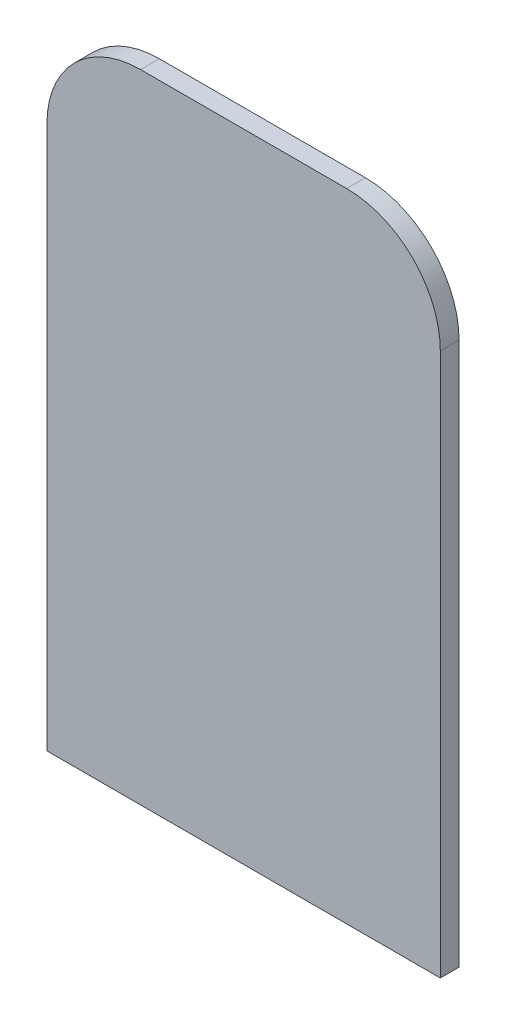
SolidWorks part; units mm, degrees
ref_plane "前视基准面" through (0, 0, 0) normal (0, 0, 1) x (1, 0, 0)
ref_plane "上视基准面" through (0, 0, 0) normal (0, 1, 0) x (1, 0, 0)
ref_plane "右视基准面" through (0, 0, 0) normal (1, 0, 0) x (0, 0, -1)
sketch "草图1" plane through (0, 0, 0) normal (0, 0, 1) x (1, 0, 0)
  line L0 (0, 0) -> (28.4707, 0) construction
  line L1 (0, 0) -> (0, 26.5422) construction
  line L2 (10.5, 0) -> (-10.5, 0)
  line L3 (-10.5, 0) -> (-10.5, 29)
  line L4 (-5.5, 34) -> (5.5, 34)
  line L5 (10.5, 0) -> (10.5, 29)
  arc A0 (-10.5, 29) -> (-5.5, 34) centre (-5.5, 29) cw
  arc A1 (10.5, 29) -> (5.5, 34) centre (5.5, 29) ccw
  point P13 (0, 0)
  point P15 (0, 34)
  dimension "D3" = 5
  dimension "D1" = 10.5
  dimension "D2" = 34
extrude "凸台-拉伸1" add sketch "草图1" along normal blind 1
